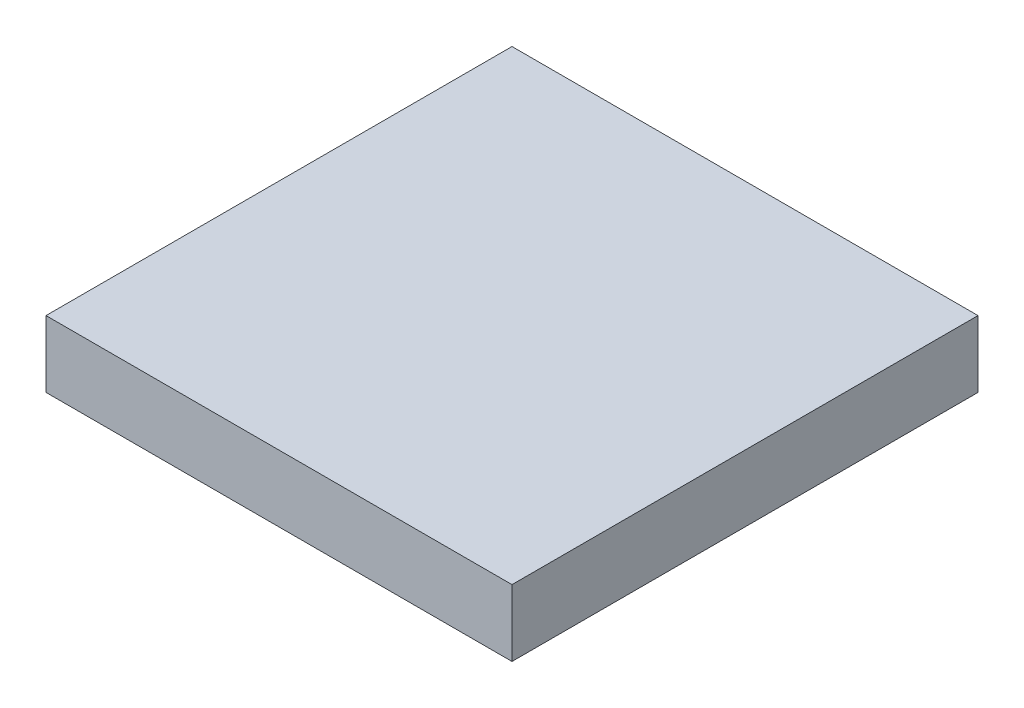
SolidWorks part; units mm, degrees
ref_plane "Front Plane" through (0, 0, 0) normal (0, 0, 1) x (1, 0, 0)
ref_plane "Top Plane" through (0, 0, 0) normal (0, 1, 0) x (1, 0, 0)
ref_plane "Right Plane" through (0, 0, 0) normal (1, 0, 0) x (0, 0, -1)
sketch "Sketch1" plane through (0, 0, 0) normal (0, 1, 0) x (1, 0, 0)
  line L1 (0, 0) -> (88.9, 0)
  line L2 (0, 0) -> (0, -88.9)
  line L3 (0, -88.9) -> (88.9, -88.9)
  line L4 (88.9, 0) -> (88.9, -88.9)
extrude "Boss-Extrude1" add sketch "Sketch1" along normal blind 12.7
sketch "Sketch3" plane through (0, 12.7, 0) normal (0, 1, 0) x (1, 0, 0)
  line L0 (44.45, -88.9) -> (44.45, 0) construction
  line L1 (0, -88.9) -> (88.9, -88.9) construction
  line L2 (88.9, 0) -> (0, 0) construction
  line L3 (88.9, -44.45) -> (0, -44.45) construction
  line L4 (88.9, -88.9) -> (88.9, 0) construction
  line L5 (0, 0) -> (0, -88.9) construction
sketch "Sketch4" plane through (0, 0, 0) normal (0, -1, 0) x (1, 0, 0)
  line L0 (44.45, 0) -> (44.45, 88.9) construction
  line L1 (88.9, 44.45) -> (0, 44.45) construction
